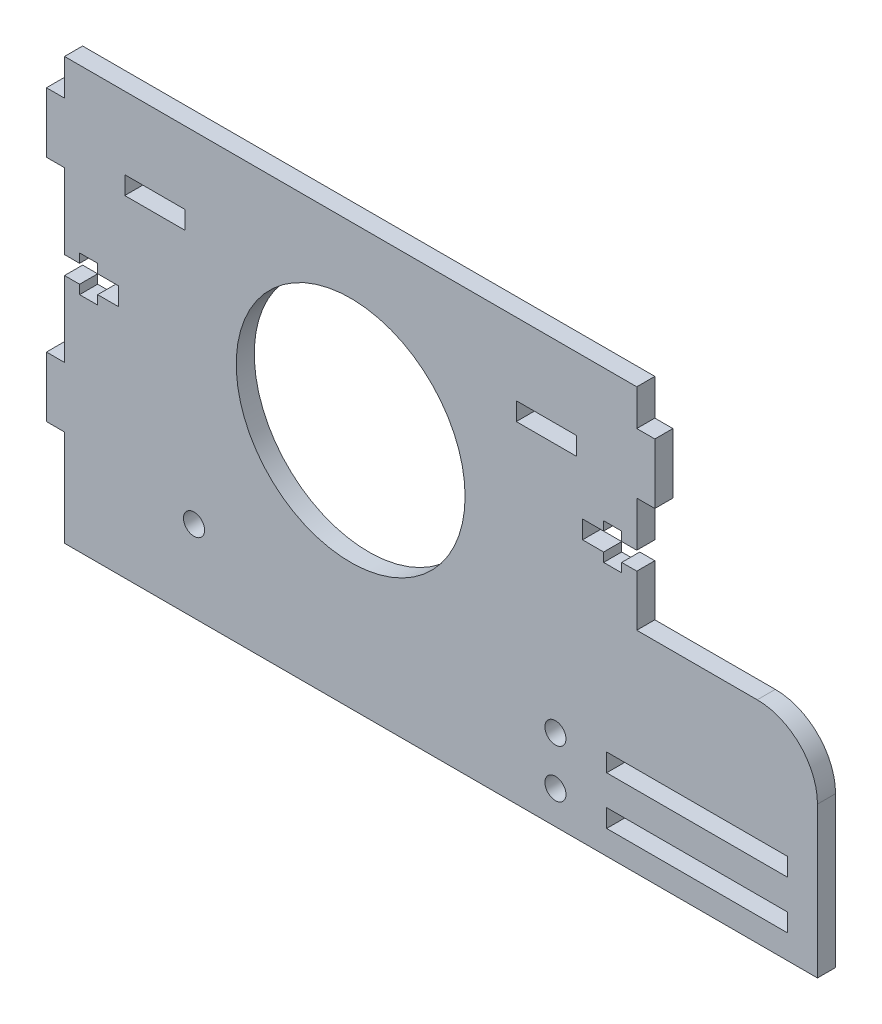
SolidWorks part; units mm, degrees
ref_plane "Front Plane" through (0, 0, 0) normal (0, 0, 1) x (1, 0, 0)
ref_plane "Top Plane" through (0, 0, 0) normal (0, 1, 0) x (1, 0, 0)
ref_plane "Right Plane" through (0, 0, 0) normal (1, 0, 0) x (0, 0, -1)
sketch "Sketch1" plane through (0, 0, 0) normal (0, 0, 1) x (1, 0, 0)
  line L1 (-47.5, 30) -> (47.5, 30)
  line L2 (-47.5, 30) -> (-47.5, 24)
  line L4 (47.5, 30) -> (47.5, 24)
  line L5 (47.5, 14) -> (47.5, 6.5)
  line L7 (47.5, -5) -> (67.5, -5)
  line L10 (77.5, -15) -> (77.5, -30)
  line L12 (-47.5, -1.5) -> (-47.5, -14)
  line L13 (42.5, -25) -> (72.5, -25)
  line L14 (42.5, -25) -> (42.5, -28)
  line L15 (42.5, -28) -> (72.5, -28)
  line L16 (72.5, -25) -> (72.5, -28)
  line L19 (-47.5, 24) -> (-50.5, 24)
  line L21 (-47.5, 14) -> (-50.5, 14)
  line L22 (-50.5, 24) -> (-50.5, 14)
  line L23 (47.5, 3.5) -> (47.5, -5)
  line L24 (45, 6.5) -> (47.5, 6.5)
  line L28 (-47.5, -14) -> (-50.5, -14)
  line L30 (-47.5, 1.5) -> (-45, 1.5)
  line L32 (-47.5, -1.5) -> (-45, -1.5)
  line L33 (-38.5, 1.5) -> (-38.5, -1.5)
  line L34 (-42, 1.5) -> (-38.5, 1.5)
  line L35 (-47.5, -24) -> (-47.5, -30)
  line L36 (-45, 3) -> (-42, 3)
  line L37 (-45, 3) -> (-45, 1.5)
  line L38 (-45, -3) -> (-42, -3)
  line L39 (-42, 3) -> (-42, 1.5)
  line L40 (-47.5, 14) -> (-47.5, 1.5)
  line L46 (38.5, 6.5) -> (42, 6.5)
  line L47 (38.5, 6.5) -> (38.5, 3.5)
  line L48 (38.5, 3.5) -> (42, 3.5)
  line L52 (45, 8) -> (42, 8)
  line L53 (45, 8) -> (45, 6.5)
  line L54 (45, 2) -> (42, 2)
  line L55 (42, 8) -> (42, 6.5)
  line L58 (-37.5, 18) -> (-27.5, 18)
  line L59 (-37.5, 18) -> (-37.5, 15)
  line L60 (-37.5, 15) -> (-27.5, 15)
  line L61 (-27.5, 18) -> (-27.5, 15)
  line L63 (42, 3.5) -> (42, 2)
  line L68 (-47.5, -24) -> (-50.5, -24)
  line L70 (-50.5, -14) -> (-50.5, -24)
  line L71 (50.5, 24) -> (47.5, 24)
  line L72 (50.5, 24) -> (50.5, 14)
  line L73 (50.5, 14) -> (47.5, 14)
  line L74 (45, 3.5) -> (47.5, 3.5)
  line L76 (27.5, 18) -> (27.5, 15)
  line L77 (37.5, 18) -> (37.5, 15)
  line L78 (27.5, 15) -> (37.5, 15)
  line L79 (27.5, 18) -> (28.178, 17.7966) construction
  line L80 (27.5, 18) -> (37.5, 18)
  line L81 (45, 3.5) -> (45, 2)
  line L82 (42.5, -33) -> (72.5, -33)
  line L84 (-47.5, -30) -> (-47.5, -40)
  line L85 (-47.5, -40) -> (77.5, -40)
  line L86 (77.5, -30) -> (77.5, -40)
  line L87 (-45, -1.5) -> (-45, -3)
  line L89 (42.5, -33) -> (42.5, -36)
  line L90 (72.5, -33) -> (72.5, -36)
  line L91 (42.5, -36) -> (72.5, -36)
  line L92 (27.5, 17.3684) -> (28.5, 18) construction
  line L94 (73.2073, -6.7886) -> (77.5, -5) construction
  line L99 (-42, -1.5) -> (-42, -3)
  line L101 (-42, -1.5) -> (-38.5, -1.5)
  circle A0 centre (0, 0) radius 19
  arc A1 (67.5, -5) -> (77.5, -15) centre (67.5, -15) cw
  circle A2 centre (-26, -26.5) radius 1.75
  circle A6 centre (34, -26.5) radius 1.75
  circle A7 centre (34, -34.5) radius 1.75
  point P0 (0, 0)
  point P8 (47.5, -17.5)
  point P16 (57.5, -26.5)
  point P21 (-43.5, 0)
  point P28 (15, -35)
  point P30 (-47.5, 19)
  point P36 (-43, 0)
  point P45 (43.5, 5)
  point P51 (43, 5)
  point P61 (-32.5, 16.5)
  dimension "D3" = 10
  dimension "D4" = 20
  dimension "D6" = 38
  dimension "D1" = 95
  dimension "D2" = 60
  dimension "D5" = 10
extrude "Boss-Extrude3" add sketch "Sketch1" along normal blind 3
